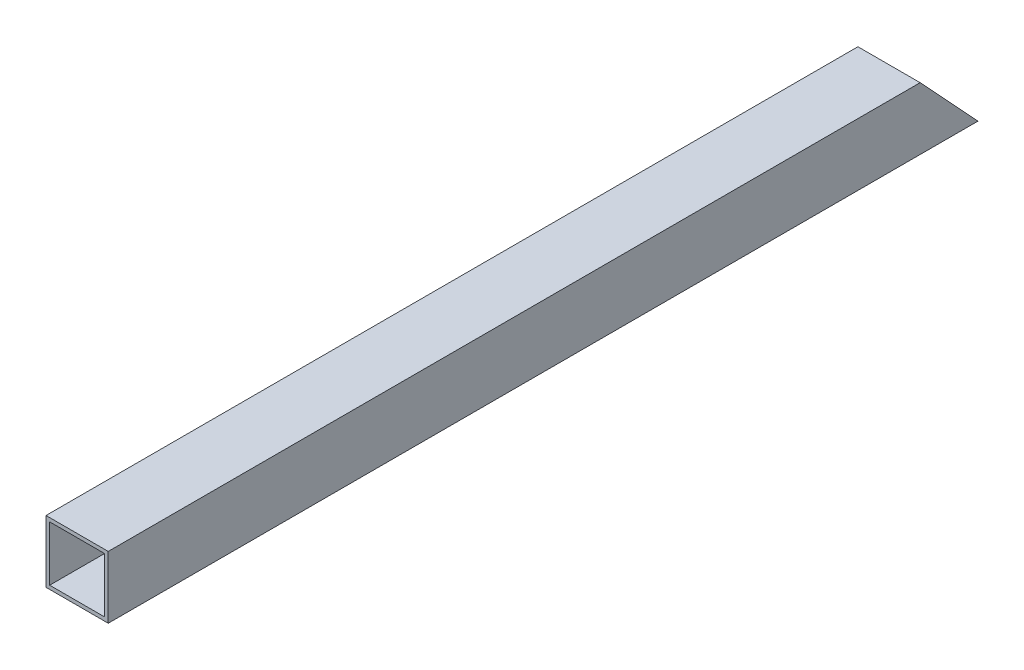
SolidWorks part; units mm, degrees
ref_plane "Front Plane" through (0, 0, 0) normal (0, 0, 1) x (1, 0, 0)
ref_plane "Top Plane" through (0, 0, 0) normal (0, 1, 0) x (1, 0, 0)
ref_plane "Right Plane" through (0, 0, 0) normal (1, 0, 0) x (0, 0, -1)
sketch "Sketch1" plane through (0, 0, 0) normal (0, 0, 1) x (1, 0, 0)
  line L1 (-12.7, -12.7) -> (12.7, -12.7)
  line L2 (-12.7, -12.7) -> (-12.7, 12.7)
  line L3 (-12.7, 12.7) -> (12.7, 12.7)
  line L4 (12.7, -12.7) -> (12.7, 12.7)
  line L5 (-12.7, -12.7) -> (12.7, 12.7) construction
  line L6 (-12.7, 12.7) -> (12.7, -12.7) construction
  line L7 (-11.2, -11.2) -> (11.2, -11.2)
  line L8 (-11.2, -11.2) -> (-11.2, 11.2)
  line L9 (-11.2, 11.2) -> (11.2, 11.2)
  line L10 (11.2, -11.2) -> (11.2, 11.2)
  line L11 (-11.2, -11.2) -> (11.2, 11.2) construction
  line L12 (-11.2, 11.2) -> (11.2, -11.2) construction
  point P0 (0, 0)
  point P6 (0, 0)
  dimension "D1" = 25.4
  dimension "D2" = 25.4
  dimension "D3" = 1.5
extrude "Boss-Extrude1" add sketch "Sketch1" along normal blind 355
sketch "Sketch3" plane through (-12.7, 0, 0) normal (-1, 0, 0) x (0, 0, 1)
  line L0 (0, -12.7) -> (23.62, 12.7)
  line L1 (355, 12.7) -> (0, 12.7) construction
  line L2 (23.62, 12.7) -> (0, 12.7)
  line L3 (0, 12.7) -> (0, -12.7)
  dimension "D1" = 23.62
extrude "Cut-Extrude2" cut sketch "Sketch3" against normal blind 25.4
